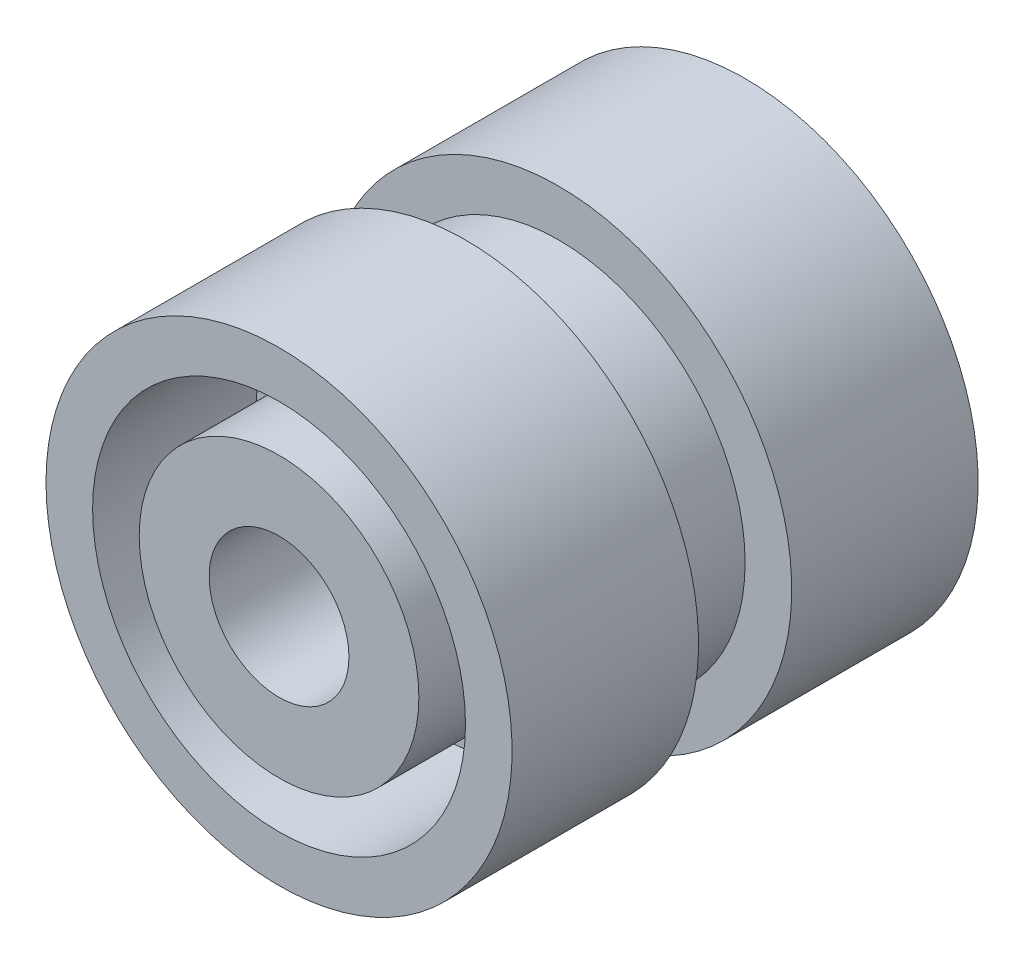
SolidWorks part; units mm, degrees
material "ABS"
ref_plane "Front Plane" through (0, 0, 0) normal (0, 0, 1) x (1, 0, 0)
ref_plane "Top Plane" through (0, 0, 0) normal (0, 1, 0) x (1, 0, 0)
ref_plane "Right Plane" through (0, 0, 0) normal (1, 0, 0) x (0, 0, -1)
sketch "Sketch1" plane through (0, 0, 0) normal (1, 0, 0) x (0, 0, -1)
  line L0 (0, 0) -> (-9.2077, 0) construction
  line L1 (0, 0) -> (-5, 0)
  line L2 (-5, 0) -> (-5, 3)
  line L3 (-5, 3) -> (-1.5, 3)
  line L4 (-1.5, 3) -> (-1.5, 4)
  line L5 (-1.5, 4) -> (-5, 4)
  line L6 (-5, 4) -> (-5, 5)
  line L7 (-5, 5) -> (-1, 5)
  line L8 (-1, 5) -> (-1, 4)
  line L9 (-1, 4) -> (1, 4)
  line L10 (0, 4) -> (0, 0) construction
  line L11 (1, 5) -> (1, 4)
  line L12 (5, 5) -> (1, 5)
  line L13 (1.5, 4) -> (5, 4)
  line L14 (5, 4) -> (5, 5)
  line L15 (1.5, 4) -> (1.5, 0)
  line L16 (1.5, 0) -> (0, 0)
  dimension "D1" = 5
  dimension "D2" = 3
  dimension "D3" = 3.5
  dimension "D4" = 1
  dimension "D5" = 3.5
  dimension "D6" = 1
  dimension "D7" = 1
  dimension "D8" = 1
revolve "Revolve1" add sketch "Sketch1" angle 360 about L0
sketch "Sketch2" plane through (0, 0, -1.5) normal (0, 0, -1) x (-1, 0, 0)
  line L0 (0, 0) -> (0, 4) construction
  line L1 (0.5, 1.9365) -> (0.5, 3.9686)
  line L2 (-0.5, 1.9365) -> (-0.5, 3.9686)
  line L3 (-0.5, 0) -> (-0.5, 4) construction
  line L4 (0.5, 0) -> (0.5, 4) construction
  line L5 (1.9365, -0.5) -> (3.9686, -0.5)
  line L6 (1.9365, 0.5) -> (3.9686, 0.5)
  line L7 (-0.5, -1.9365) -> (-0.5, -3.9686)
  line L8 (0.5, -1.9365) -> (0.5, -3.9686)
  line L9 (-1.9365, 0.5) -> (-3.9686, 0.5)
  line L10 (-1.9365, -0.5) -> (-3.9686, -0.5)
  circle A0 centre (0, 0) radius 4 construction
  arc A1 (-3.9686, 0.5) -> (-3.9686, -0.5) centre (0, 0) ccw
  arc A2 (-1.9365, -0.5) -> (-0.5, -1.9365) centre (0, 0) ccw
  arc A3 (-0.5, -3.9686) -> (0.5, -3.9686) centre (0, 0) ccw
  arc A4 (3.9686, -0.5) -> (3.9686, 0.5) centre (0, 0) ccw
  arc A5 (0.5, 3.9686) -> (-0.5, 3.9686) centre (0, 0) ccw
  arc A6 (0.5, -1.9365) -> (1.9365, -0.5) centre (0, 0) ccw
  arc A7 (1.9365, 0.5) -> (0.5, 1.9365) centre (0, 0) ccw
  arc A8 (-0.5, 1.9365) -> (-1.9365, 0.5) centre (0, 0) ccw
  dimension "D1" = 4
  dimension "D2" = 0.5
  dimension "D3" = 0.5
  dimension "D4" = 4
extrude "Boss-Extrude1" add sketch "Sketch2" along normal blind 2
sketch "Sketch3" plane through (0, 0, 5) normal (0, 0, 1) x (1, 0, 0)
  circle A0 centre (0, 0) radius 1.5
  dimension "D1" = 3
extrude "Cut-Extrude1" cut sketch "Sketch3" against normal blind 8
